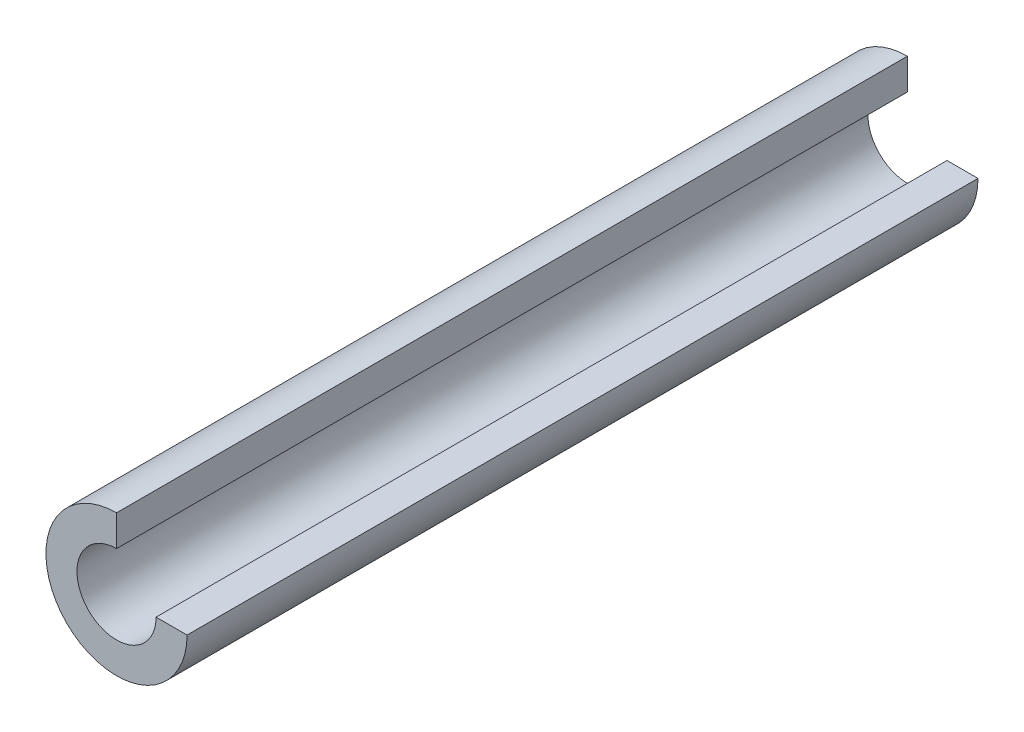
SolidWorks part; units mm, degrees
ref_plane "Front Plane" through (0, 0, 0) normal (0, 0, 1) x (1, 0, 0)
ref_plane "Top Plane" through (0, 0, 0) normal (0, 1, 0) x (1, 0, 0)
ref_plane "Right Plane" through (0, 0, 0) normal (1, 0, 0) x (0, 0, -1)
sketch "Sketch1" plane through (0, 0, 0) normal (0, 0, 1) x (1, 0, 0)
  line L6 (0, 2.55) -> (0, 4.55)
  line L7 (2.55, 0) -> (4.55, 0)
  arc A4 (0, 2.55) -> (2.55, 0) centre (0, 0) ccw
  arc A5 (0, 4.55) -> (4.55, 0) centre (0, 0) ccw
  point P7 (0, 4.55)
  point P8 (0, 2.55)
  point P9 (4.55, 0)
  point P10 (2.55, 0)
  dimension "D1" = 2
  dimension "D2" = 2.55
extrude "Boss-Extrude1" add sketch "Sketch1" along normal blind 40
other "Move Face1" face at (-0.3676, -0.3676, 40) parameters "D1"=11
